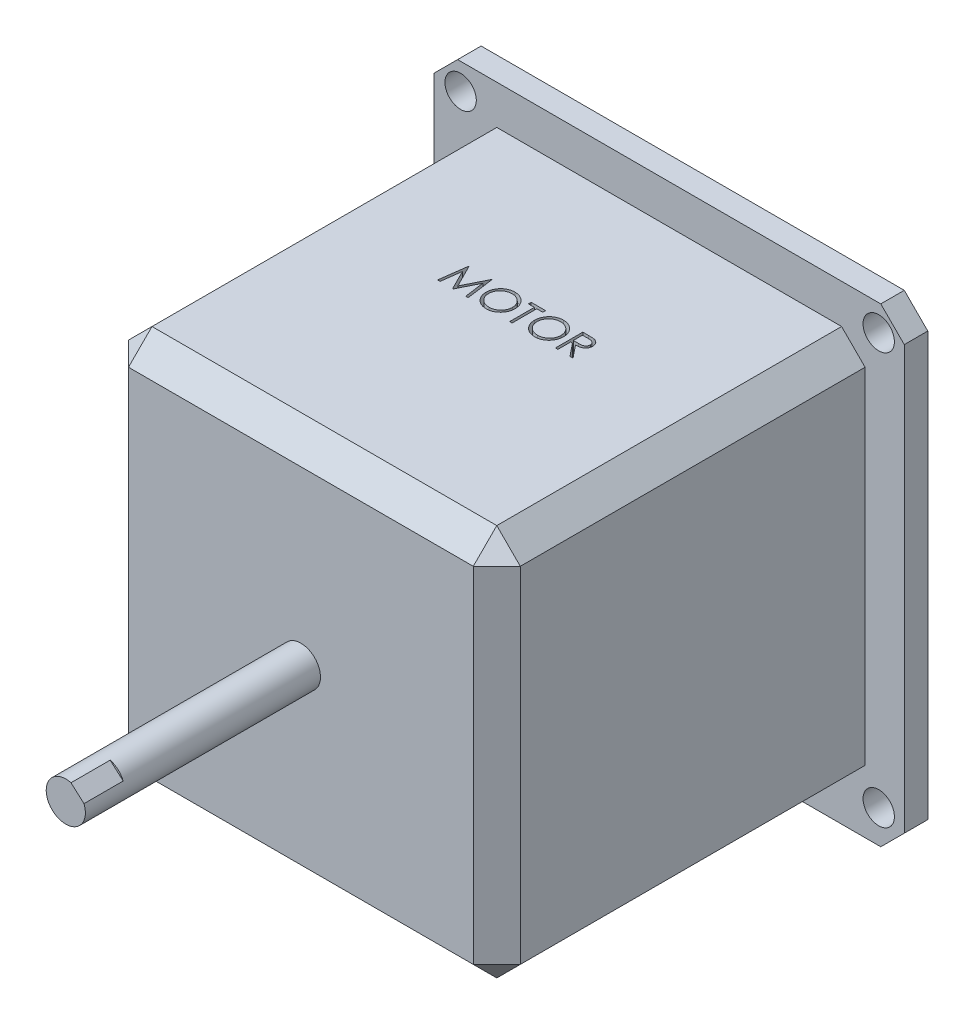
SolidWorks part; units mm, degrees
ref_plane "Front Plane" through (0, 0, 0) normal (0, 0, 1) x (1, 0, 0)
ref_plane "Top Plane" through (0, 0, 0) normal (0, 1, 0) x (1, 0, 0)
ref_plane "Right Plane" through (0, 0, 0) normal (1, 0, 0) x (0, 0, -1)
sketch "Sketch1" plane through (0, 0, 0) normal (0, 0, 1) x (1, 0, 0)
  line L1 (-25, 25) -> (25, 25)
  line L2 (-25, 25) -> (-25, -25)
  line L3 (-25, -25) -> (25, -25)
  line L4 (25, 25) -> (25, -25)
  line L5 (-25, 25) -> (25, -25) construction
  line L6 (-25, -25) -> (25, 25) construction
  point P0 (0, 0)
  dimension "D1" = 50
  dimension "D2" = 50
extrude "Boss-Extrude1" add sketch "Sketch1" along normal mid plane 50
chamfer "Chamfer1" distance 3 12 edges at (-25, 0, 25) (0, 25, 25) (-25, 25, 0) (-25, -25, 0) (0, -25, 25) (0, 25, -25) (-25, 0, -25) (0, -25, -25) (25, -25, 0) (25, 0, 25) (25, 25, 0) (25, 0, -25)
sketch "Sketch2" plane through (0, 0, 0) normal (0, 0, 1) x (1, 0, 0)
  circle A0 centre (0, 0) radius 2.5
  dimension "D1" = 5
extrude "Boss-Extrude2" add sketch "Sketch2" along normal blind 50
sketch "Sketch3" plane through (0, 25, 0) normal (0, 1, 0) x (1, 0, 0)
  text T0 "MOTOR"
extrude "Cut-Extrude1" cut sketch "Sketch3" against normal blind 3
sketch "Sketch4" plane through (0, 0, 50) normal (0, 0, 1) x (1, 0, 0)
  line L0 (0.6642, 2.4102) -> (2.3208, 0.9294)
  circle A1 centre (0, 0) radius 2.5
  arc A2 (0.6642, 2.4102) -> (2.3208, 0.9294) centre (0, 0) ccw
  dimension "D1" = 0
extrude "Boss-Extrude3" add sketch "Sketch4" along normal blind 5
sketch "Sketch5" plane through (0, 0, -25) normal (0, 0, -1) x (-1, 0, 0)
  line L0 (-22, 25) -> (22, 25) construction
  line L1 (-30, 30) -> (30, 30)
  line L2 (-30, 30) -> (-30, -30)
  line L3 (-30, -30) -> (30, -30)
  line L4 (30, 30) -> (30, -30)
  line L5 (22, -25) -> (-22, -25) construction
  line L7 (-25, -22) -> (-25, 22) construction
  line L8 (25, 22) -> (25, -22) construction
  dimension "D1" = 5
  dimension "D2" = 5
  dimension "D3" = 5
  dimension "D4" = 5
extrude "Boss-Extrude4" add sketch "Sketch5" against normal blind 3
hole_wizard "Ø4.0mm Dowel Hole1" positions "Sketch7" profile "Sketch6" hole size "Ø4.0" standard "ANSI Metric" end condition through all
sketch "Sketch7" plane through (0, 0, -25) normal (0, 0, -1) x (-1, 0, 0)
  point P0 (26.6163, 26.6785)
  point P2 (-26.7407, 26.6785)
  point P4 (-26.7407, -25.8079)
  point P6 (26.6163, -25.8079)
sketch "Sketch6" plane through (-26.6163, 26.6785, -25) normal (1, 0, 0) x (0, 1, 0)
  line L0 (0, 0) -> (0, 80)
  line L1 (0, 80) -> (2, 80)
  line L2 (2, 80) -> (2, 0)
  line L5 (2, 0) -> (0, 0)
  line L11 (0, -6.35) -> (0, 107.95) construction
  dimension "Thru Hole Dia." = 4
  dimension "Thru Hole Depth" = 80
chamfer "Chamfer2" distance 3 angle 45 4 edges at (30, -30, -23.5) (-30, -30, -23.5) (-30, 30, -23.5) (30, 30, -23.5)
